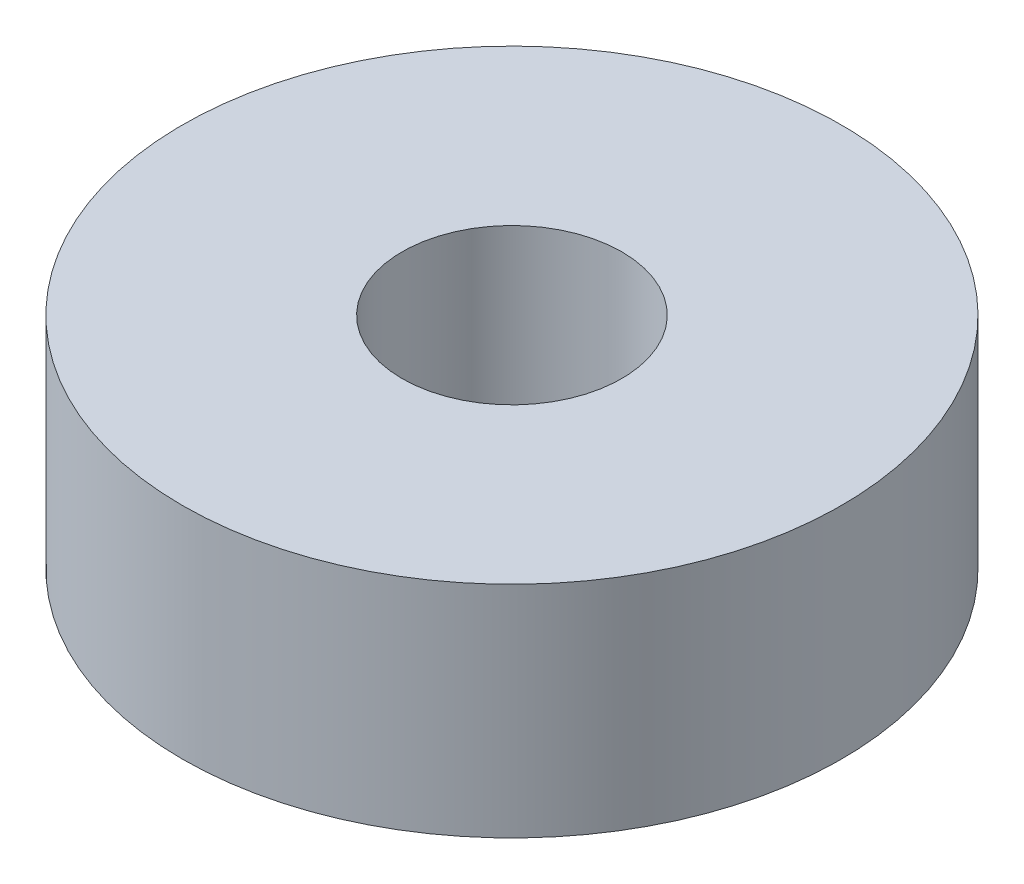
SolidWorks part; units mm, degrees
material "Alloy Steel"
ref_plane "Front Plane" through (0, 0, 0) normal (0, 0, 1) x (1, 0, 0)
ref_plane "Top Plane" through (0, 0, 0) normal (0, 1, 0) x (1, 0, 0)
ref_plane "Right Plane" through (0, 0, 0) normal (1, 0, 0) x (0, 0, -1)
sketch "Sketch1" plane through (0, 0, 0) normal (0, 1, 0) x (1, 0, 0)
  circle A0 centre (0, 0) radius 6
  circle A1 centre (0, 0) radius 2
  dimension "D1" = 4
  dimension "D2" = 12
extrude "Boss-Extrude1" add sketch "Sketch1" along normal blind 4
